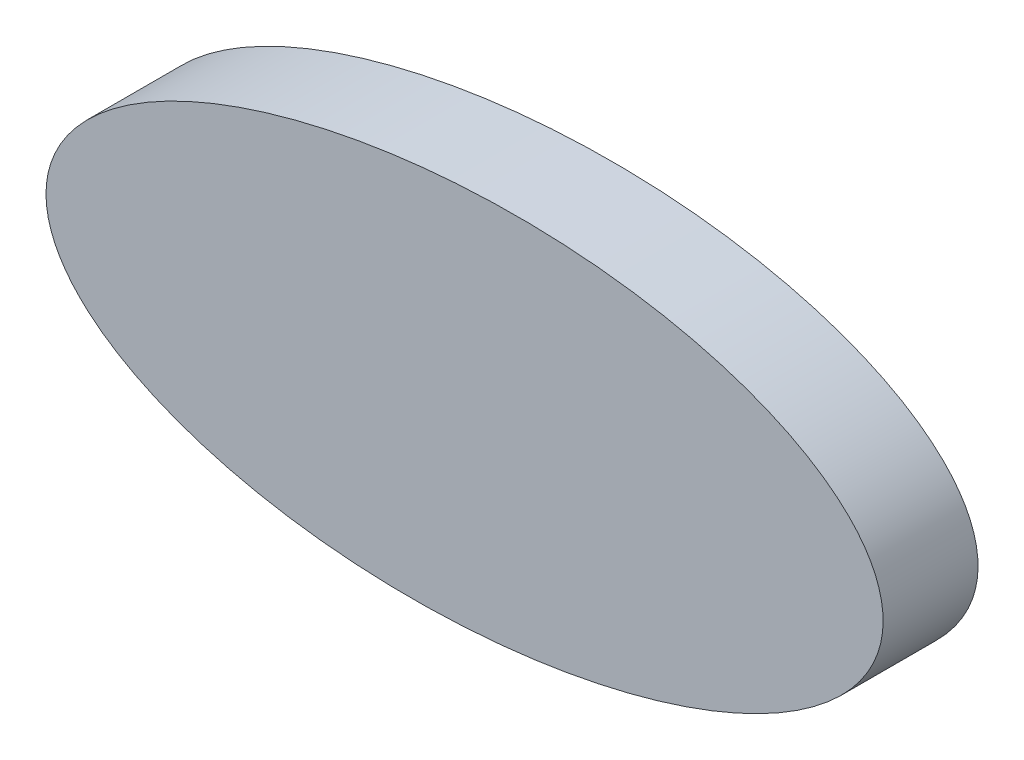
SolidWorks part; units mm, degrees
ref_plane "Front Plane" through (0, 0, 0) normal (0, 0, 1) x (1, 0, 0)
ref_plane "Top Plane" through (0, 0, 0) normal (0, 1, 0) x (1, 0, 0)
ref_plane "Right Plane" through (0, 0, 0) normal (1, 0, 0) x (0, 0, -1)
sketch "Sketch1" plane through (0, 0, 0) normal (0, 0, 1) x (1, 0, 0)
  ellipse E0 centre (0, 0) end of major axis (44.0772, 3.235) minor radius 20.0056
  point P1 (0, 0)
  point P7 (0, 0)
  dimension "D1" = 88.1544
  dimension "D2" = 39.9038
  dimension "D3" = 44.1958
extrude "Boss-Extrude1" add sketch "Sketch1" along normal blind 10
